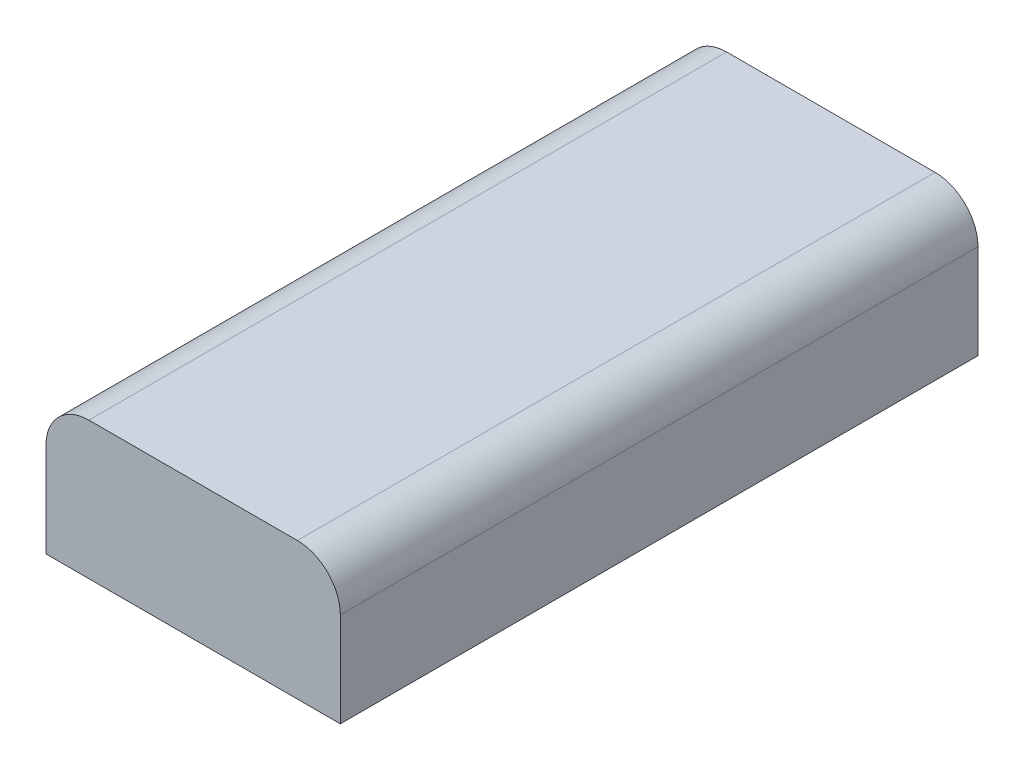
SolidWorks part; units mm, degrees
ref_plane "Front Plane" through (0, 0, 0) normal (0, 0, 1) x (1, 0, 0)
ref_plane "Top Plane" through (0, 0, 0) normal (0, 1, 0) x (1, 0, 0)
ref_plane "Right Plane" through (0, 0, 0) normal (1, 0, 0) x (0, 0, -1)
sketch "Sketch2" plane through (0, 0, 0) normal (0, 0, 1) x (1, 0, 0)
  line L0 (0, 0) -> (24, 0)
  line L1 (24, 0) -> (24, 7.7)
  line L2 (20.5, 11.2) -> (3.5, 11.2)
  line L3 (0, 7.7) -> (0, 0)
  arc A0 (24, 7.7) -> (20.5, 11.2) centre (20.5, 7.7) ccw
  arc A1 (3.5, 11.2) -> (0, 7.7) centre (3.5, 7.7) ccw
  dimension "D1" = 24
  dimension "D2" = 11.2
  dimension "D3" = 17
extrude "Boss-Extrude1" add sketch "Sketch2" along normal blind 52
